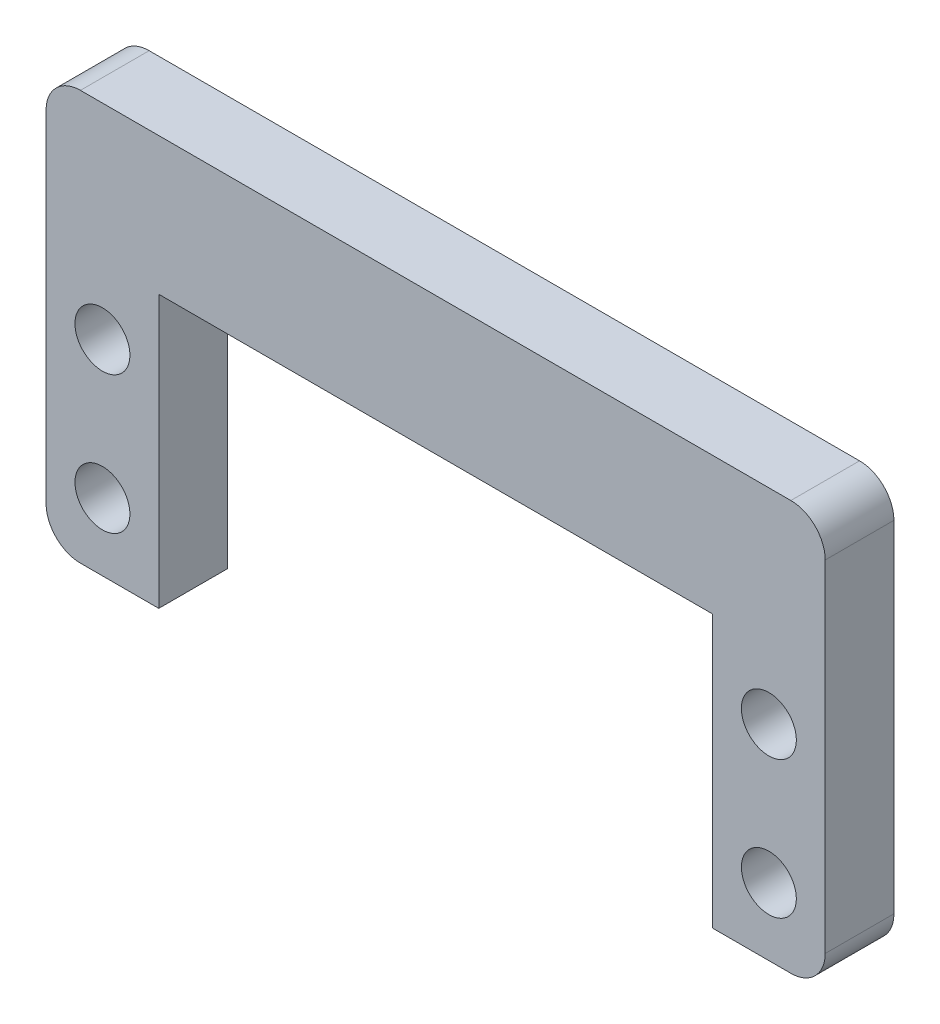
SolidWorks part; units mm, degrees
ref_plane "Alzado" through (0, 0, 0) normal (0, 0, 1) x (1, 0, 0)
ref_plane "Planta" through (0, 0, 0) normal (0, 1, 0) x (1, 0, 0)
ref_plane "Vista lateral" through (0, 0, 0) normal (1, 0, 0) x (0, 0, -1)
sketch "Sketch1" plane through (0, 0, 0) normal (0, 0, 1) x (1, 0, 0)
  line L0 (-24.25, 0) -> (24.25, 0) construction
  line L1 (24.25, -5) -> (24.25, 5) construction
  line L2 (-24.25, -5) -> (-24.25, 5) construction
  line L3 (-24.25, 5) -> (-24.25, 9.9) construction
  line L4 (-24.25, -5) -> (-20.15, -5) construction
  line L5 (-24.25, -5) -> (-24.25, -9.9) construction
  line L6 (-24.25, -5) -> (-28.35, -5) construction
  line L7 (0, -5) -> (0, 5) construction
  line L8 (-20.15, -9.9) -> (-25.85, -9.9)
  line L9 (-20.15, -9.9) -> (-20.15, 9.9)
  line L10 (-20.15, 9.9) -> (-28.35, 9.9)
  line L11 (-28.35, -7.4) -> (-28.35, 9.9)
  line L12 (20.15, 9.9) -> (28.35, 9.9)
  line L13 (28.35, -7.4) -> (28.35, 9.9)
  line L14 (20.15, -9.9) -> (25.85, -9.9)
  line L15 (20.15, -9.9) -> (20.15, 9.9)
  line L17 (-28.35, 9.9) -> (28.35, 9.9)
  line L18 (-28.35, 9.9) -> (-28.35, 17.4)
  line L19 (-25.85, 19.9) -> (25.85, 19.9)
  line L20 (28.35, 9.9) -> (28.35, 17.4)
  circle A0 centre (24.25, -5) radius 2
  circle A1 centre (-24.25, -5) radius 2
  circle A2 centre (-24.25, 5) radius 2
  circle A3 centre (24.25, 5) radius 2
  arc A4 (-28.35, 17.4) -> (-25.85, 19.9) centre (-25.85, 17.4) cw
  arc A5 (25.85, 19.9) -> (28.35, 17.4) centre (25.85, 17.4) cw
  arc A6 (28.35, -7.4) -> (25.85, -9.9) centre (25.85, -7.4) cw
  arc A7 (-25.85, -9.9) -> (-28.35, -7.4) centre (-25.85, -7.4) cw
  point P4 (0, 0)
  point P8 (24.25, 0)
  point P11 (-24.25, 0)
  point P28 (0, 0)
  point P36 (-28.35, 19.9)
  point P41 (28.35, -9.9)
  point P44 (-28.35, -9.9)
  dimension "D2" = 4
  dimension "D6" = 56.7
  dimension "D7" = 48.5
  dimension "D8" = 5
  dimension "D9" = 48.5
  dimension "D10" = 4.9
  dimension "D17" = 4.9
  dimension "D18" = 2.5
  dimension "D1" = 5
  dimension "D3" = 10
  dimension "D4" = 2
  dimension "D11" = 4.1
  dimension "D12" = 4.9
  dimension "D13" = 4.1
  dimension "D14" = 19.8
  dimension "D15" = 8.2
  dimension "D16" = 4.1
  dimension "D5" = 2
extrude "Boss-Extrude1" add sketch "Sketch1" along normal blind 5 contours A7 L8 L9 L10 L11 A1 A2 | A5 L19 A4 L18 L10 L17 L12 L20 | A6 L13 L12 L15 L14 A3 A0
